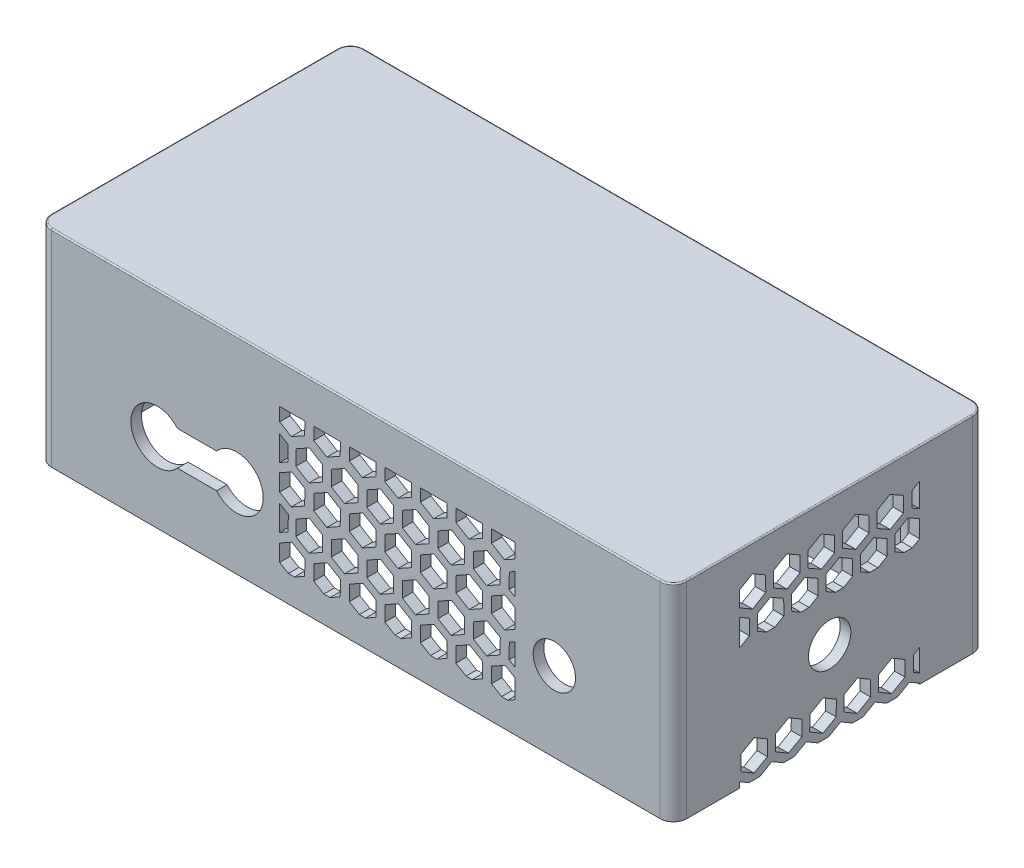
SolidWorks part; units mm, degrees
ref_plane "Front Plane" through (0, 0, 0) normal (0, 0, 1) x (1, 0, 0)
ref_plane "Top Plane" through (0, 0, 0) normal (0, 1, 0) x (1, 0, 0)
ref_plane "Right Plane" through (0, 0, 0) normal (1, 0, 0) x (0, 0, -1)
sketch "Sketch1" plane through (0, 0, 0) normal (0, 1, 0) x (1, 0, 0)
  line L1 (120, -59) -> (-120, -59)
  line L2 (120, -59) -> (120, 59)
  line L3 (120, 59) -> (-120, 59)
  line L4 (-120, -59) -> (-120, 59)
  line L5 (120, -59) -> (-120, 59) construction
  line L6 (120, 59) -> (-120, -59) construction
  point P0 (0, 0)
  dimension "D1" = 240
  dimension "D2" = 118
extrude "Boss-Extrude1" add sketch "Sketch1" along normal blind 78
sketch "Sketch2" plane through (0, 0, 0) normal (0, 1, 0) x (1, 0, 0)
  line L1 (-116, -55) -> (116, -55)
  line L2 (-116, -55) -> (-116, 55)
  line L3 (-116, 55) -> (116, 55)
  line L4 (116, -55) -> (116, 55)
  line L5 (-116, -55) -> (116, 55) construction
  line L6 (-116, 55) -> (116, -55) construction
  point P0 (0, 0)
  dimension "D1" = 232
  dimension "D2" = 110
extrude "Cut-Extrude1" cut sketch "Sketch2" along normal blind 70
sketch "Sketch3" plane through (0, 0, 0) normal (0, 1, 0) x (1, 0, 0)
  line L1 (-120, -59) -> (-106, -59)
  line L2 (-120, -59) -> (-120, -37)
  line L3 (-120, -37) -> (-106, -37)
  line L4 (-106, -59) -> (-106, -37)
  line L5 (-120, 59) -> (-106, 59)
  line L6 (-120, 59) -> (-120, 37)
  line L7 (-120, 37) -> (-106, 37)
  line L8 (-106, 59) -> (-106, 37)
  line L9 (120, -59) -> (106, -59)
  line L10 (120, -59) -> (120, -37)
  line L11 (120, -37) -> (106, -37)
  line L12 (106, -59) -> (106, -37)
  line L13 (120, 59) -> (106, 59)
  line L14 (120, 59) -> (120, 37)
  line L15 (120, 37) -> (106, 37)
  line L16 (106, 59) -> (106, 37)
  dimension "D1" = 22
  dimension "D2" = 14
  dimension "D3" = 14
  dimension "D4" = 22
  dimension "D5" = 22
  dimension "D6" = 14
  dimension "D7" = 14
  dimension "D8" = 22
extrude "Boss-Extrude2" add sketch "Sketch3" along normal blind 77.2
fillet "Fillet1" radius 2 8 edges at (106, 35, -55) (116, 35, -37) (116, 35, 37) (106, 35, 55) (-106, 35, -55) (-116, 35, -37) (-106, 35, 55) (-116, 35, 37)
fillet "Fillet2" radius 6.5 4 edges at (106, 35, -37) (106, 35, 37) (-106, 35, -37) (-106, 35, 37)
fillet "Fillet3" radius 5 4 edges at (120, 39, 59) (120, 39, -59) (-120, 39, -59) (-120, 39, 59)
sketch "Sketch4" plane through (0, 0, 0) normal (0, 0, 1) x (1, 0, 0)
  line L0 (-67.4007, 23.5) -> (-52.5993, 23.5)
  line L1 (-120, 78) -> (-120, 0) construction
  line L2 (-136.1714, 30) -> (133.1398, 30) construction
  line L7 (-67.4007, 36.5) -> (-52.5993, 36.5)
  circle A0 centre (75, 30) radius 8
  arc A1 (-67.4007, 36.5) -> (-67.4007, 23.5) centre (-75, 30) ccw
  arc A2 (-52.5993, 23.5) -> (-52.5993, 36.5) centre (-45, 30) ccw
  dimension "D1" = 45
  dimension "D2" = 195
extrude "Side Lidar and Sonar holes" cut sketch "Sketch4" against normal through all both and the other way through all
sketch "Sketch5" plane through (0, 0, 0) normal (0, 0, 1) x (1, 0, 0)
  line L0 (-12.5736, 29.0672) -> (-17.5522, 32.0521)
  line L1 (-19.2427, 17.9082) -> (-24.1944, 20.877)
  line L2 (-17.5522, 32.0521) -> (-22.5992, 29.2483)
  line L3 (-28.7882, 11.9716) -> (-28.7882, 63)
  line L4 (-28.7882, 63) -> (60.0514, 63)
  line L5 (-25.4998, 10) -> (57.3982, 10)
  line L6 (60.0514, 11.474) -> (60.0514, 63)
  line L7 (-24.1944, 20.877) -> (-28.7882, 18.3249)
  line L8 (-25.6128, 52.1399) -> (-28.7882, 54.0438)
  line L9 (-28.7882, 11.9716) -> (-25.4998, 10)
  line L10 (-23.1818, 10) -> (-19.338, 12.1354)
  line L11 (-19.338, 12.1354) -> (-19.2427, 17.9082)
  line L12 (-22.5992, 29.2483) -> (-22.6944, 23.4756)
  line L13 (-22.6944, 23.4756) -> (-17.7158, 20.4906)
  line L14 (-17.7158, 20.4906) -> (-12.6689, 23.2944)
  line L15 (-12.6689, 23.2944) -> (-12.5736, 29.0672)
  line L16 (0.8564, 29.0672) -> (-4.1222, 32.0521)
  line L17 (-5.8127, 17.9082) -> (-10.7644, 20.877)
  line L18 (-4.1222, 32.0521) -> (-9.1692, 29.2483)
  line L19 (-10.7644, 20.877) -> (-15.8114, 18.0732)
  line L20 (-15.8114, 18.0732) -> (-15.9066, 12.3004)
  line L21 (-15.9066, 12.3004) -> (-12.0698, 10)
  line L22 (-9.7518, 10) -> (-5.908, 12.1354)
  line L23 (-5.908, 12.1354) -> (-5.8127, 17.9082)
  line L24 (-9.1692, 29.2483) -> (-9.2644, 23.4756)
  line L25 (-9.2644, 23.4756) -> (-4.2858, 20.4906)
  line L26 (-4.2858, 20.4906) -> (0.7611, 23.2944)
  line L27 (0.7611, 23.2944) -> (0.8564, 29.0672)
  line L28 (14.2864, 29.0672) -> (9.3078, 32.0521)
  line L29 (7.6173, 17.9082) -> (2.6656, 20.877)
  line L30 (9.3078, 32.0521) -> (4.2608, 29.2483)
  line L31 (2.6656, 20.877) -> (-2.3814, 18.0732)
  line L32 (-2.3814, 18.0732) -> (-2.4766, 12.3004)
  line L33 (-2.4766, 12.3004) -> (1.3602, 10)
  line L34 (3.6782, 10) -> (7.522, 12.1354)
  line L35 (7.522, 12.1354) -> (7.6173, 17.9082)
  line L36 (4.2608, 29.2483) -> (4.1656, 23.4756)
  line L37 (4.1656, 23.4756) -> (9.1442, 20.4906)
  line L38 (9.1442, 20.4906) -> (14.1911, 23.2944)
  line L39 (14.1911, 23.2944) -> (14.2864, 29.0672)
  line L40 (27.7164, 29.0672) -> (22.7378, 32.0521)
  line L41 (21.0473, 17.9082) -> (16.0956, 20.877)
  line L42 (22.7378, 32.0521) -> (17.6908, 29.2483)
  line L43 (16.0956, 20.877) -> (11.0486, 18.0732)
  line L44 (11.0486, 18.0732) -> (10.9534, 12.3004)
  line L45 (10.9534, 12.3004) -> (14.7902, 10)
  line L46 (17.1082, 10) -> (20.952, 12.1354)
  line L47 (20.952, 12.1354) -> (21.0473, 17.9082)
  line L48 (17.6908, 29.2483) -> (17.5956, 23.4756)
  line L49 (17.5956, 23.4756) -> (22.5742, 20.4906)
  line L50 (22.5742, 20.4906) -> (27.6211, 23.2944)
  line L51 (27.6211, 23.2944) -> (27.7164, 29.0672)
  line L52 (41.1464, 29.0672) -> (36.1678, 32.0521)
  line L53 (34.4773, 17.9082) -> (29.5256, 20.877)
  line L54 (36.1678, 32.0521) -> (31.1208, 29.2483)
  line L55 (29.5256, 20.877) -> (24.4786, 18.0732)
  line L56 (24.4786, 18.0732) -> (24.3834, 12.3004)
  line L57 (24.3834, 12.3004) -> (28.2202, 10)
  line L58 (30.5382, 10) -> (34.382, 12.1354)
  line L59 (34.382, 12.1354) -> (34.4773, 17.9082)
  line L60 (31.1208, 29.2483) -> (31.0256, 23.4756)
  line L61 (31.0256, 23.4756) -> (36.0042, 20.4906)
  line L62 (36.0042, 20.4906) -> (41.0511, 23.2944)
  line L63 (41.0511, 23.2944) -> (41.1464, 29.0672)
  line L64 (54.5764, 29.0672) -> (49.5978, 32.0521)
  line L65 (47.9073, 17.9082) -> (42.9556, 20.877)
  line L66 (49.5978, 32.0521) -> (44.5508, 29.2483)
  line L67 (42.9556, 20.877) -> (37.9086, 18.0732)
  line L68 (37.9086, 18.0732) -> (37.8134, 12.3004)
  line L69 (37.8134, 12.3004) -> (41.6502, 10)
  line L70 (43.9682, 10) -> (47.812, 12.1354)
  line L71 (47.812, 12.1354) -> (47.9073, 17.9082)
  line L72 (44.5508, 29.2483) -> (44.4556, 23.4756)
  line L73 (44.4556, 23.4756) -> (49.4342, 20.4906)
  line L74 (49.4342, 20.4906) -> (54.4811, 23.2944)
  line L75 (54.4811, 23.2944) -> (54.5764, 29.0672)
  line L77 (60.0514, 18.6791) -> (56.3856, 20.877)
  line L78 (60.0514, 30.3986) -> (57.9808, 29.2483)
  line L79 (56.3856, 20.877) -> (51.3386, 18.0732)
  line L80 (51.3386, 18.0732) -> (51.2434, 12.3004)
  line L81 (51.2434, 12.3004) -> (55.0802, 10)
  line L82 (57.3982, 10) -> (60.0514, 11.474)
  line L84 (57.9808, 29.2483) -> (57.8856, 23.4756)
  line L85 (57.8856, 23.4756) -> (60.0514, 22.177)
  line L87 (-28.7882, 44.656) -> (-25.7081, 46.3672)
  line L88 (0.8564, 52.0672) -> (-4.1222, 55.0521)
  line L89 (-5.8127, 40.9082) -> (-10.7644, 43.877)
  line L90 (-4.1222, 55.0521) -> (-9.1692, 52.2483)
  line L91 (-10.7644, 43.877) -> (-15.8114, 41.0732)
  line L92 (-15.8114, 41.0732) -> (-15.9066, 35.3004)
  line L93 (-15.9066, 35.3004) -> (-10.9549, 32.3316)
  line L94 (-10.9549, 32.3316) -> (-5.908, 35.1354)
  line L95 (-5.908, 35.1354) -> (-5.8127, 40.9082)
  line L96 (-9.1692, 52.2483) -> (-9.2644, 46.4756)
  line L97 (-9.2644, 46.4756) -> (-4.2858, 43.4906)
  line L98 (-4.2858, 43.4906) -> (0.7611, 46.2944)
  line L99 (0.7611, 46.2944) -> (0.8564, 52.0672)
  line L100 (14.2864, 52.0672) -> (9.3078, 55.0521)
  line L101 (7.6173, 40.9082) -> (2.6656, 43.877)
  line L102 (9.3078, 55.0521) -> (4.2608, 52.2483)
  line L103 (2.6656, 43.877) -> (-2.3814, 41.0732)
  line L104 (-2.3814, 41.0732) -> (-2.4766, 35.3004)
  line L105 (-2.4766, 35.3004) -> (2.4751, 32.3316)
  line L106 (2.4751, 32.3316) -> (7.522, 35.1354)
  line L107 (7.522, 35.1354) -> (7.6173, 40.9082)
  line L108 (4.2608, 52.2483) -> (4.1656, 46.4756)
  line L109 (4.1656, 46.4756) -> (9.1442, 43.4906)
  line L110 (9.1442, 43.4906) -> (14.1911, 46.2944)
  line L111 (14.1911, 46.2944) -> (14.2864, 52.0672)
  line L112 (27.7164, 52.0672) -> (22.7378, 55.0521)
  line L113 (21.0473, 40.9082) -> (16.0956, 43.877)
  line L114 (22.7378, 55.0521) -> (17.6908, 52.2483)
  line L115 (16.0956, 43.877) -> (11.0486, 41.0732)
  line L116 (11.0486, 41.0732) -> (10.9534, 35.3004)
  line L117 (10.9534, 35.3004) -> (15.9051, 32.3316)
  line L118 (15.9051, 32.3316) -> (20.952, 35.1354)
  line L119 (20.952, 35.1354) -> (21.0473, 40.9082)
  line L120 (17.6908, 52.2483) -> (17.5956, 46.4756)
  line L121 (17.5956, 46.4756) -> (22.5742, 43.4906)
  line L122 (22.5742, 43.4906) -> (27.6211, 46.2944)
  line L123 (27.6211, 46.2944) -> (27.7164, 52.0672)
  line L124 (41.1464, 52.0672) -> (36.1678, 55.0521)
  line L125 (34.4773, 40.9082) -> (29.5256, 43.877)
  line L126 (36.1678, 55.0521) -> (31.1208, 52.2483)
  line L127 (29.5256, 43.877) -> (24.4786, 41.0732)
  line L128 (24.4786, 41.0732) -> (24.3834, 35.3004)
  line L129 (24.3834, 35.3004) -> (29.3351, 32.3316)
  line L130 (29.3351, 32.3316) -> (34.382, 35.1354)
  line L131 (34.382, 35.1354) -> (34.4773, 40.9082)
  line L132 (31.1208, 52.2483) -> (31.0256, 46.4756)
  line L133 (31.0256, 46.4756) -> (36.0042, 43.4906)
  line L134 (36.0042, 43.4906) -> (41.0511, 46.2944)
  line L135 (41.0511, 46.2944) -> (41.1464, 52.0672)
  line L136 (54.5764, 52.0672) -> (49.5978, 55.0521)
  line L137 (47.9073, 40.9082) -> (42.9556, 43.877)
  line L138 (49.5978, 55.0521) -> (44.5508, 52.2483)
  line L139 (42.9556, 43.877) -> (37.9086, 41.0732)
  line L140 (37.9086, 41.0732) -> (37.8134, 35.3004)
  line L141 (37.8134, 35.3004) -> (42.7651, 32.3316)
  line L142 (42.7651, 32.3316) -> (47.812, 35.1354)
  line L143 (47.812, 35.1354) -> (47.9073, 40.9082)
  line L144 (44.5508, 52.2483) -> (44.4556, 46.4756)
  line L145 (44.4556, 46.4756) -> (49.4342, 43.4906)
  line L146 (49.4342, 43.4906) -> (54.4811, 46.2944)
  line L147 (54.4811, 46.2944) -> (54.5764, 52.0672)
  line L148 (-25.7081, 46.3672) -> (-25.6128, 52.1399)
  line L149 (60.0514, 41.6791) -> (56.3856, 43.877)
  line L150 (60.0514, 53.3986) -> (57.9808, 52.2483)
  line L151 (56.3856, 43.877) -> (51.3386, 41.0732)
  line L152 (51.3386, 41.0732) -> (51.2434, 35.3004)
  line L153 (51.2434, 35.3004) -> (56.1951, 32.3316)
  line L154 (56.1951, 32.3316) -> (60.0514, 34.474)
  line L155 (-25.5041, 29.3213) -> (-28.7882, 31.2903)
  line L156 (57.9808, 52.2483) -> (57.8856, 46.4756)
  line L157 (57.8856, 46.4756) -> (60.0514, 45.177)
  line L163 (-28.7882, 21.7771) -> (-25.5994, 23.5486)
  line L164 (-15.8291, 63) -> (-15.9066, 58.3004)
  line L165 (-15.9066, 58.3004) -> (-10.9549, 55.3316)
  line L166 (-10.9549, 55.3316) -> (-5.908, 58.1354)
  line L167 (-5.908, 58.1354) -> (-5.8277, 63)
  line L173 (-25.5994, 23.5486) -> (-25.5041, 29.3213)
  line L176 (-2.3991, 63) -> (-2.4766, 58.3004)
  line L177 (-2.4766, 58.3004) -> (2.4751, 55.3316)
  line L178 (2.4751, 55.3316) -> (7.522, 58.1354)
  line L179 (7.522, 58.1354) -> (7.6023, 63)
  line L188 (11.0309, 63) -> (10.9534, 58.3004)
  line L189 (10.9534, 58.3004) -> (15.9051, 55.3316)
  line L190 (15.9051, 55.3316) -> (20.952, 58.1354)
  line L191 (20.952, 58.1354) -> (21.0323, 63)
  line L200 (24.4609, 63) -> (24.3834, 58.3004)
  line L201 (24.3834, 58.3004) -> (29.3351, 55.3316)
  line L202 (29.3351, 55.3316) -> (34.382, 58.1354)
  line L203 (34.382, 58.1354) -> (34.4623, 63)
  line L212 (37.8909, 63) -> (37.8134, 58.3004)
  line L213 (37.8134, 58.3004) -> (42.7651, 55.3316)
  line L214 (42.7651, 55.3316) -> (47.812, 58.1354)
  line L215 (47.812, 58.1354) -> (47.8923, 63)
  line L224 (51.3209, 63) -> (51.2434, 58.3004)
  line L225 (51.2434, 58.3004) -> (56.1951, 55.3316)
  line L226 (56.1951, 55.3316) -> (60.0514, 57.474)
  line L232 (-12.5736, 52.0672) -> (-17.5522, 55.0521)
  line L233 (-19.2427, 40.9082) -> (-24.1944, 43.877)
  line L234 (-17.5522, 55.0521) -> (-22.5992, 52.2483)
  line L235 (-24.1944, 43.877) -> (-28.7882, 41.3249)
  line L237 (-28.7882, 34.9716) -> (-24.3849, 32.3316)
  line L238 (-24.3849, 32.3316) -> (-19.338, 35.1354)
  line L239 (-19.338, 35.1354) -> (-19.2427, 40.9082)
  line L240 (-22.5992, 52.2483) -> (-22.6944, 46.4756)
  line L241 (-22.6944, 46.4756) -> (-17.7158, 43.4906)
  line L242 (-17.7158, 43.4906) -> (-12.6689, 46.2944)
  line L243 (-12.6689, 46.2944) -> (-12.5736, 52.0672)
  line L249 (-28.7882, 57.9716) -> (-24.3849, 55.3316)
  line L250 (-24.3849, 55.3316) -> (-19.338, 58.1354)
  line L251 (-19.338, 58.1354) -> (-19.2577, 63)
  line L256 (61.2896, 15.0218) -> (61.3373, 17.9082) [skipped]
  line L257 (68.0064, 29.0672) -> (63.0278, 32.0521) [skipped]
  line L258 (62.8642, 20.4906) -> (67.9111, 23.2944) [skipped]
  line L259 (67.9111, 23.2944) -> (68.0064, 29.0672) [skipped]
  line L260 (61.2896, 38.0218) -> (61.3373, 40.9082) [skipped]
  line L261 (68.0064, 52.0672) -> (63.0278, 55.0521) [skipped]
  line L262 (67.9111, 46.2944) -> (68.0064, 52.0672) [skipped]
  line L263 (62.8642, 43.4906) -> (67.9111, 46.2944) [skipped]
  line L264 (-29.2414, 18.0732) -> (-29.289, 15.1868) [skipped]
  line L265 (-24.1944, 66.877) -> (-26.7179, 65.4751) [skipped]
  line L266 (-19.2427, 63.9082) -> (-21.7186, 65.3926) [skipped]
  line L267 (-10.7644, 66.877) -> (-13.2879, 65.4751) [skipped]
  line L268 (-5.8127, 63.9082) -> (-8.2886, 65.3926) [skipped]
  line L269 (2.6656, 66.877) -> (0.1421, 65.4751) [skipped]
  line L270 (7.6173, 63.9082) -> (2.6656, 66.877) [skipped]
  line L271 (16.0956, 66.877) -> (13.5721, 65.4751) [skipped]
  line L272 (21.0473, 63.9082) -> (18.5714, 65.3926) [skipped]
  line L273 (29.5256, 66.877) -> (27.0021, 65.4751) [skipped]
  line L274 (34.4773, 63.9082) -> (32.0014, 65.3926) [skipped]
  line L275 (42.9556, 66.877) -> (40.4321, 65.4751) [skipped]
  line L276 (47.9073, 63.9082) -> (45.4314, 65.3926) [skipped]
  line L277 (56.3856, 66.877) -> (53.8621, 65.4751) [skipped]
  line L278 (61.3373, 63.9082) -> (58.8614, 65.3926) [skipped]
  line L279 (61.242, 58.1354) -> (61.2896, 61.0218) [skipped]
  line L280 (0.8564, 75.0672) -> (-4.1222, 78.0521) [skipped]
  line L281 (-4.1222, 78.0521) -> (-9.1692, 75.2483) [skipped]
  line L282 (-9.1692, 75.2483) -> (-9.2644, 69.4756) [skipped]
  line L283 (-9.2644, 69.4756) -> (-4.2858, 66.4906) [skipped]
  line L284 (-4.2858, 66.4906) -> (0.7611, 69.2944) [skipped]
  line L285 (0.7611, 69.2944) -> (0.8564, 75.0672) [skipped]
  line L286 (14.2864, 75.0672) -> (9.3078, 78.0521) [skipped]
  line L287 (9.3078, 78.0521) -> (4.2608, 75.2483) [skipped]
  line L288 (4.2608, 75.2483) -> (4.1656, 69.4756) [skipped]
  line L289 (4.1656, 69.4756) -> (9.1442, 66.4906) [skipped]
  line L290 (9.1442, 66.4906) -> (14.1911, 69.2944) [skipped]
  line L291 (14.1911, 69.2944) -> (14.2864, 75.0672) [skipped]
  line L292 (27.7164, 75.0672) -> (22.7378, 78.0521) [skipped]
  line L293 (22.7378, 78.0521) -> (17.6908, 75.2483) [skipped]
  line L294 (17.6908, 75.2483) -> (17.5956, 69.4756) [skipped]
  line L295 (17.5956, 69.4756) -> (22.5742, 66.4906) [skipped]
  line L296 (22.5742, 66.4906) -> (27.6211, 69.2944) [skipped]
  line L297 (27.6211, 69.2944) -> (27.7164, 75.0672) [skipped]
  line L298 (41.1464, 75.0672) -> (36.1678, 78.0521) [skipped]
  line L299 (36.1678, 78.0521) -> (31.1208, 75.2483) [skipped]
  line L300 (31.1208, 75.2483) -> (31.0256, 69.4756) [skipped]
  line L301 (31.0256, 69.4756) -> (36.0042, 66.4906) [skipped]
  line L302 (36.0042, 66.4906) -> (41.0511, 69.2944) [skipped]
  line L303 (41.0511, 69.2944) -> (41.1464, 75.0672) [skipped]
  line L304 (54.5764, 75.0672) -> (49.5978, 78.0521) [skipped]
  line L305 (49.5978, 78.0521) -> (44.5508, 75.2483) [skipped]
  line L306 (44.5508, 75.2483) -> (44.4556, 69.4756) [skipped]
  line L307 (44.4556, 69.4756) -> (49.4342, 66.4906) [skipped]
  line L308 (49.4342, 66.4906) -> (54.4811, 69.2944) [skipped]
  line L309 (54.4811, 69.2944) -> (54.5764, 75.0672) [skipped]
  line L310 (68.0064, 75.0672) -> (63.0278, 78.0521) [skipped]
  line L311 (63.0278, 78.0521) -> (57.9808, 75.2483) [skipped]
  line L312 (57.9808, 75.2483) -> (57.8856, 69.4756) [skipped]
  line L313 (57.8856, 69.4756) -> (62.8642, 66.4906) [skipped]
  line L314 (62.8642, 66.4906) -> (67.9111, 69.2944) [skipped]
  line L315 (67.9111, 69.2944) -> (68.0064, 75.0672) [skipped]
  line L316 (-12.5736, 75.0672) -> (-17.5522, 78.0521) [skipped]
  line L317 (-17.5522, 78.0521) -> (-22.5992, 75.2483) [skipped]
  line L318 (-22.5992, 75.2483) -> (-22.6944, 69.4756) [skipped]
  line L319 (-22.6944, 69.4756) -> (-17.7158, 66.4906) [skipped]
  line L320 (-17.7158, 66.4906) -> (-12.6689, 69.2944) [skipped]
  line L321 (-12.6689, 69.2944) -> (-12.5736, 75.0672) [skipped]
  arc A0 (-28.7882, 12.9218) -> (-28.7882, 17.2868) centre (-24.2897, 15.1043) ccw construction
  circle A1 centre (-17.6475, 26.2794) radius 5 construction
  circle A2 centre (-10.8597, 15.1043) radius 5 construction
  circle A3 centre (-4.2175, 26.2794) radius 5 construction
  circle A4 centre (2.5703, 15.1043) radius 5 construction
  circle A5 centre (9.2125, 26.2794) radius 5 construction
  circle A6 centre (16.0003, 15.1043) radius 5 construction
  circle A7 centre (22.6425, 26.2794) radius 5 construction
  circle A8 centre (29.4303, 15.1043) radius 5 construction
  circle A9 centre (36.0725, 26.2794) radius 5 construction
  circle A10 centre (42.8603, 15.1043) radius 5 construction
  circle A11 centre (49.5025, 26.2794) radius 5 construction
  arc A12 (60.0514, 18.3988) -> (60.0514, 11.8098) centre (56.2903, 15.1043) ccw construction
  arc A13 (60.0514, 30.3659) -> (60.0514, 22.193) centre (62.9325, 26.2794) ccw construction
  circle A14 centre (-10.8597, 38.1043) radius 5 construction
  circle A15 centre (-4.2175, 49.2794) radius 5 construction
  circle A16 centre (2.5703, 38.1043) radius 5 construction
  circle A17 centre (9.2125, 49.2794) radius 5 construction
  circle A18 centre (16.0003, 38.1043) radius 5 construction
  circle A19 centre (22.6425, 49.2794) radius 5 construction
  circle A20 centre (29.4303, 38.1043) radius 5 construction
  circle A21 centre (36.0725, 49.2794) radius 5 construction
  circle A22 centre (42.8603, 38.1043) radius 5 construction
  circle A23 centre (49.5025, 49.2794) radius 5 construction
  arc A24 (60.0514, 41.3988) -> (60.0514, 34.8098) centre (56.2903, 38.1043) ccw construction
  arc A25 (60.0514, 53.3659) -> (60.0514, 45.193) centre (62.9325, 49.2794) ccw construction
  arc A26 (-15.4864, 63) -> (-6.233, 63) centre (-10.8597, 61.1043) ccw construction
  arc A28 (-2.0564, 63) -> (7.197, 63) centre (2.5703, 61.1043) ccw construction
  arc A30 (11.3736, 63) -> (20.627, 63) centre (16.0003, 61.1043) ccw construction
  arc A32 (24.8036, 63) -> (34.057, 63) centre (29.4303, 61.1043) ccw construction
  arc A34 (38.2336, 63) -> (47.487, 63) centre (42.8603, 61.1043) ccw construction
  arc A36 (51.6636, 63) -> (60.0514, 57.8098) centre (56.2903, 61.1043) ccw construction
  arc A38 (-28.7882, 35.9218) -> (-28.7882, 40.2868) centre (-24.2897, 38.1043) ccw construction
  circle A39 centre (-17.6475, 49.2794) radius 5 construction
  arc A40 (-28.7882, 58.9218) -> (-19.663, 63) centre (-24.2897, 61.1043) ccw construction
  arc A42 (-28.7882, 44.7266) -> (-28.7882, 53.9778) centre (-30.6867, 49.3522) ccw construction
  arc A43 (-28.7882, 21.8649) -> (-28.7882, 31.2023) centre (-30.578, 26.5336) ccw construction
  circle A46 centre (-4.2175, 72.2794) radius 5 construction
  circle A47 centre (9.2125, 72.2794) radius 5 construction
  circle A48 centre (22.6425, 72.2794) radius 5 construction
  circle A49 centre (36.0725, 72.2794) radius 5 construction
  circle A50 centre (49.5025, 72.2794) radius 5 construction
  circle A51 centre (62.9325, 72.2794) radius 5 construction
  circle A52 centre (-17.6475, 72.2794) radius 5 construction
  point P20 (-21.7186, 19.3926)
  dimension "D1" = 3
  dimension "D2" = 1.5
  dimension "D4" = 2.5986
  dimension "D5" = 1.6222
  dimension "D7" = 7
  dimension "D8" = 3
extrude "Side honeycomb" cut sketch "Sketch5" against normal through all both and the other way through all contours L10 L11 L1 L7 L3 L9 L5 | L14 L15 L0 L2 L12 L13 | L238 L239 L233 L235 L3 L237 | L242 L243 L232 L234 L240 L241 | L250 L251 L4 L3 L249 | L166 L167 L4 L164 L165 | L178 L179 L4 L176 L177 | L98 L99 L88 L90 L96 L97 | L106 L107 L101 L103 L104 L105 | L94 L95 L89 L91 L92 L93 | L22 L23 L17 L19 L20 L21 L5 | L34 L35 L29 L31 L32 L33 L5 | L38 L39 L28 L30 L36 L37 | L118 L119 L113 L115 L116 L117 | L110 L111 L100 L102 L108 L109 | L190 L191 L4 L188 L189 | L122 L123 L112 L114 L120 L121 | L130 L131 L125 L127 L128 L129 | L50 L51 L40 L42 L48 L49 | L46 L47 L41 L43 L44 L45 L5 | L58 L59 L53 L55 L56 L57 L5 | L62 L63 L52 L54 L60 L61 | L142 L143 L137 L139 L140 L141 | L134 L135 L124 L126 L132 L133 | L202 L203 L4 L200 L201 | L214 L215 L4 L212 L213 | L225 L226 L6 L4 L224 | L146 L147 L136 L138 L144 L145 | L153 L154 L6 L149 L151 L152 | L74 L75 L64 L66 L72 L73 | L70 L71 L65 L67 L68 L69 L5 | L5 L82 L6 L77 L79 L80 L81 | L84 L85 L6 L78 | L156 L157 L6 L150 | L87 L148 L8 L3 | L163 L173 L155 L3 | L24 L25 L26 L27 L16 L18
sketch "Sketch6" plane through (0, 0, 0) normal (1, 0, 0) x (0, 0, -1)
  line L0 (59, 78) -> (59, 0) construction
  line L1 (-54, 0) -> (54, 0) construction
  line L2 (67.1373, 30) -> (-67.1373, 30) construction
  circle A0 centre (0, 30) radius 8
  dimension "D1" = 59
  dimension "D2" = 30
extrude "Back Sonar" cut sketch "Sketch6" along normal blind 145
sketch "Sketch7" plane through (0, 0, 0) normal (1, 0, 0) x (0, 0, -1)
  line L0 (-34, 64.9032) -> (-34, 58.965)
  line L2 (-54, 0) -> (54, 0) construction
  line L3 (-34, 46) -> (-33.7633, 46)
  line L4 (34, 0) -> (34, 0.3416)
  line L7 (-59, 0) -> (-59, 78) construction
  line L8 (59, 78) -> (59, 0) construction
  line L9 (34, 47.6163) -> (34, 54.1712)
  line L11 (17.8738, 59.0369) -> (22.89, 56.1785)
  line L12 (24.693, 47.9651) -> (28.1414, 46)
  line L13 (31.2367, 46) -> (34, 47.6163)
  line L15 (34, 54.1712) -> (29.644, 56.6534)
  line L16 (29.644, 56.6534) -> (24.6604, 53.7385)
  line L17 (24.6604, 53.7385) -> (24.693, 47.9651)
  line L18 (22.89, 56.1785) -> (27.8736, 59.0934)
  line L19 (27.8736, 59.0934) -> (27.841, 64.8668)
  line L20 (27.841, 64.8668) -> (22.8248, 67.7253)
  line L21 (22.8248, 67.7253) -> (17.8412, 64.8103)
  line L22 (17.8412, 64.8103) -> (17.8738, 59.0369)
  line L23 (4.8738, 59.0369) -> (9.89, 56.1785)
  line L24 (11.693, 47.9651) -> (15.1414, 46)
  line L25 (18.2367, 46) -> (21.6928, 48.0215)
  line L26 (21.6928, 48.0215) -> (21.6602, 53.795)
  line L27 (21.6602, 53.795) -> (16.644, 56.6534)
  line L28 (16.644, 56.6534) -> (11.6604, 53.7385)
  line L29 (11.6604, 53.7385) -> (11.693, 47.9651)
  line L30 (9.89, 56.1785) -> (14.8736, 59.0934)
  line L31 (14.8736, 59.0934) -> (14.841, 64.8668)
  line L32 (14.841, 64.8668) -> (9.8248, 67.7253)
  line L33 (9.8248, 67.7253) -> (4.8412, 64.8103)
  line L34 (4.8412, 64.8103) -> (4.8738, 59.0369)
  line L35 (-8.1262, 59.0369) -> (-3.11, 56.1785)
  line L36 (-1.307, 47.9651) -> (2.1414, 46)
  line L37 (5.2367, 46) -> (8.6928, 48.0215)
  line L38 (8.6928, 48.0215) -> (8.6602, 53.795)
  line L39 (8.6602, 53.795) -> (3.644, 56.6534)
  line L40 (3.644, 56.6534) -> (-1.3396, 53.7385)
  line L41 (-1.3396, 53.7385) -> (-1.307, 47.9651)
  line L42 (-3.11, 56.1785) -> (1.8736, 59.0934)
  line L43 (1.8736, 59.0934) -> (1.841, 64.8668)
  line L44 (1.841, 64.8668) -> (-3.1752, 67.7253)
  line L45 (-3.1752, 67.7253) -> (-8.1588, 64.8103)
  line L46 (-8.1588, 64.8103) -> (-8.1262, 59.0369)
  line L47 (-21.1262, 59.0369) -> (-16.11, 56.1785)
  line L48 (-14.307, 47.9651) -> (-10.8586, 46)
  line L49 (-7.7633, 46) -> (-4.3072, 48.0215)
  line L50 (-4.3072, 48.0215) -> (-4.3398, 53.795)
  line L51 (-4.3398, 53.795) -> (-9.356, 56.6534)
  line L52 (-9.356, 56.6534) -> (-14.3396, 53.7385)
  line L53 (-14.3396, 53.7385) -> (-14.307, 47.9651)
  line L54 (-16.11, 56.1785) -> (-11.1264, 59.0934)
  line L55 (-11.1264, 59.0934) -> (-11.159, 64.8668)
  line L56 (-11.159, 64.8668) -> (-16.1752, 67.7253)
  line L57 (-16.1752, 67.7253) -> (-21.1588, 64.8103)
  line L58 (-21.1588, 64.8103) -> (-21.1262, 59.0369)
  line L59 (-34, 58.965) -> (-29.11, 56.1785)
  line L60 (-27.307, 47.9651) -> (-23.8586, 46)
  line L61 (-20.7633, 46) -> (-17.3072, 48.0215)
  line L62 (-17.3072, 48.0215) -> (-17.3398, 53.795)
  line L63 (-17.3398, 53.795) -> (-22.356, 56.6534)
  line L64 (-22.356, 56.6534) -> (-27.3396, 53.7385)
  line L65 (-27.3396, 53.7385) -> (-27.307, 47.9651)
  line L66 (-29.11, 56.1785) -> (-24.1264, 59.0934)
  line L67 (-24.1264, 59.0934) -> (-24.159, 64.8668)
  line L68 (-24.159, 64.8668) -> (-29.1752, 67.7253)
  line L69 (-29.1752, 67.7253) -> (-34, 64.9032)
  line L70 (31.1586, 64.8181) -> (31.1822, 59.0447)
  line L71 (31.1822, 59.0447) -> (34, 57.4332)
  line L73 (-33.7633, 46) -> (-30.3072, 48.0215)
  line L74 (-30.3072, 48.0215) -> (-30.3398, 53.795)
  line L75 (-30.3398, 53.795) -> (-34, 55.8807)
  line L78 (34, 66.4742) -> (31.1586, 64.8181)
  line L79 (-34, 55.8807) -> (-34, 46)
  line L80 (-23.8586, 46) -> (-20.7633, 46)
  line L81 (-10.8586, 46) -> (-7.7633, 46)
  line L82 (2.1414, 46) -> (5.2367, 46)
  line L83 (15.1414, 46) -> (18.2367, 46)
  line L86 (28.1414, 46) -> (31.2367, 46)
  line L87 (34, 57.4332) -> (34, 66.4742)
  line L89 (18.5253, 10.9146) -> (18.4841, 5.1412)
  line L98 (34, 0.3416) -> (30.1804, 2.5833)
  line L99 (30.1804, 2.5833) -> (25.6313, 0)
  line L100 (18.4841, 5.1412) -> (23.4633, 2.2188)
  line L101 (23.4633, 2.2188) -> (28.4838, 5.0698)
  line L102 (28.4838, 5.0698) -> (28.525, 10.8432)
  line L103 (28.525, 10.8432) -> (23.5457, 13.7656)
  line L104 (23.5457, 13.7656) -> (18.5253, 10.9146)
  line L105 (5.5253, 10.9146) -> (5.4841, 5.1412)
  line L112 (21.5821, 0) -> (17.1804, 2.5833)
  line L113 (17.1804, 2.5833) -> (12.6313, 0)
  line L114 (5.4841, 5.1412) -> (10.4633, 2.2188)
  line L115 (10.4633, 2.2188) -> (15.4838, 5.0698)
  line L116 (15.4838, 5.0698) -> (15.525, 10.8432)
  line L117 (15.525, 10.8432) -> (10.5457, 13.7656)
  line L118 (10.5457, 13.7656) -> (5.5253, 10.9146)
  line L119 (-7.4747, 10.9146) -> (-7.5159, 5.1412)
  line L126 (8.5821, 0) -> (4.1804, 2.5833)
  line L127 (4.1804, 2.5833) -> (-0.3687, 0)
  line L128 (-7.5159, 5.1412) -> (-2.5367, 2.2188)
  line L129 (-2.5367, 2.2188) -> (2.4838, 5.0698)
  line L130 (2.4838, 5.0698) -> (2.525, 10.8432)
  line L131 (2.525, 10.8432) -> (-2.4543, 13.7656)
  line L132 (-2.4543, 13.7656) -> (-7.4747, 10.9146)
  line L133 (-20.4747, 10.9146) -> (-20.5159, 5.1412)
  line L138 (-4.4179, 0) -> (-8.8196, 2.5833)
  line L139 (-8.8196, 2.5833) -> (-13.3687, 0)
  line L140 (-20.5159, 5.1412) -> (-15.5367, 2.2188)
  line L141 (-15.5367, 2.2188) -> (-10.5162, 5.0698)
  line L142 (-10.5162, 5.0698) -> (-10.475, 10.8432)
  line L143 (-10.475, 10.8432) -> (-15.4543, 13.7656)
  line L146 (-15.4543, 13.7656) -> (-20.4747, 10.9146)
  line L147 (-33.4747, 10.9146) -> (-33.5159, 5.1412)
  line L148 (-34, 2.1023) -> (-34, 0)
  line L149 (34, 3.6732) -> (34, 12.0902)
  line L152 (-17.4179, 0) -> (-21.8196, 2.5833)
  line L153 (-21.8196, 2.5833) -> (-26.3687, 0)
  line L154 (-33.5159, 5.1412) -> (-28.5367, 2.2188)
  line L155 (7.3819, 80.6077) -> (9.89, 79.1784) [skipped]
  line L156 (9.89, 79.1784) -> (12.3818, 80.6359) [skipped]
  line L157 (27.1522, 78.1959) -> (24.6604, 76.7385) [skipped]
  line L158 (21.6602, 76.7949) -> (19.1521, 78.2242) [skipped]
  line L159 (14.1522, 78.1959) -> (11.6604, 76.7385) [skipped]
  line L160 (34.6602, 76.7949) -> (32.1521, 78.2242) [skipped]
  line L161 (20.3819, 80.6077) -> (22.89, 79.1784) [skipped]
  line L162 (25.3818, 80.6359) -> (27.8737, 82.0934) [skipped]
  line L163 (17.8412, 87.8103) -> (17.8575, 84.9236) [skipped]
  line L164 (22.8248, 90.7253) -> (17.8412, 87.8103) [skipped]
  line L165 (27.841, 87.8668) -> (25.3329, 89.296) [skipped]
  line L166 (27.8573, 84.9801) -> (27.841, 87.8668) [skipped]
  line L168 (24.6767, 73.8518) -> (24.693, 70.9651) [skipped]
  line L170 (11.6767, 73.8518) -> (11.693, 70.9651) [skipped]
  line L172 (-1.3233, 73.8518) -> (-1.307, 70.9651) [skipped]
  line L174 (-14.3233, 73.8518) -> (-14.307, 70.9651) [skipped]
  line L176 (-40.3233, 73.8518) -> (-40.307, 70.9651) [skipped]
  line L177 (-37.8478, 78.1959) -> (-40.3396, 76.7385) [skipped]
  line L178 (-30.3398, 76.7949) -> (-32.8479, 78.2242) [skipped]
  line L179 (-24.8478, 78.1959) -> (-27.3396, 76.7385) [skipped]
  line L180 (14.8573, 84.9801) -> (14.841, 87.8668) [skipped]
  line L181 (14.841, 87.8668) -> (9.8248, 90.7253) [skipped]
  line L182 (9.8248, 90.7253) -> (4.8412, 87.8103) [skipped]
  line L183 (4.8412, 87.8103) -> (4.8738, 82.0369) [skipped]
  line L184 (-8.1262, 82.0369) -> (-5.6181, 80.6077) [skipped]
  line L185 (8.6602, 76.7949) -> (3.644, 79.6534) [skipped]
  line L186 (3.644, 79.6534) -> (-1.3396, 76.7384) [skipped]
  line L187 (-0.6182, 80.6359) -> (1.8737, 82.0934) [skipped]
  line L188 (1.8736, 82.0934) -> (1.841, 87.8668) [skipped]
  line L189 (1.841, 87.8668) -> (-3.1752, 90.7253) [skipped]
  line L190 (-3.1752, 90.7253) -> (-8.1588, 87.8103) [skipped]
  line L191 (-8.1588, 87.8103) -> (-8.1262, 82.0369) [skipped]
  line L192 (-21.1262, 82.0369) -> (-18.6181, 80.6077) [skipped]
  line L193 (-4.3398, 76.7949) -> (-6.8479, 78.2242) [skipped]
  line L194 (-11.8478, 78.1959) -> (-14.3396, 76.7385) [skipped]
  line L195 (-13.6182, 80.6359) -> (-11.1263, 82.0934) [skipped]
  line L196 (-11.1264, 82.0934) -> (-11.159, 87.8668) [skipped]
  line L197 (-11.159, 87.8668) -> (-16.1752, 90.7253) [skipped]
  line L198 (-16.1752, 90.7253) -> (-21.1588, 87.8103) [skipped]
  line L199 (-21.1588, 87.8103) -> (-21.1262, 82.0369) [skipped]
  line L200 (-34.1262, 82.0369) -> (-29.11, 79.1784) [skipped]
  line L201 (-17.3398, 76.7949) -> (-19.8479, 78.2242) [skipped]
  line L202 (-29.11, 79.1784) -> (-24.1264, 82.0934) [skipped]
  line L203 (-24.1264, 82.0934) -> (-24.159, 87.8668) [skipped]
  line L204 (-24.159, 87.8668) -> (-29.1752, 90.7253) [skipped]
  line L205 (-29.1752, 90.7253) -> (-34.1588, 87.8103) [skipped]
  line L206 (-34.1588, 87.8103) -> (-34.1262, 82.0369) [skipped]
  line L207 (-47.1262, 82.0369) -> (-42.11, 79.1784) [skipped]
  line L208 (-42.11, 79.1784) -> (-37.1264, 82.0934) [skipped]
  line L209 (-37.1264, 82.0934) -> (-37.159, 87.8668) [skipped]
  line L210 (-37.159, 87.8668) -> (-42.1752, 90.7253) [skipped]
  line L211 (-42.1752, 90.7253) -> (-47.1588, 87.8103) [skipped]
  line L212 (-47.1588, 87.8103) -> (-47.1262, 82.0369) [skipped]
  line L213 (-27.3233, 73.8518) -> (-27.307, 70.9651) [skipped]
  line L215 (-37.8478, 55.1959) -> (-40.3396, 53.7385) [skipped]
  line L216 (-40.3233, 50.8518) -> (-40.307, 47.9651) [skipped]
  line L217 (-40.307, 47.9651) -> (-35.2908, 45.1066) [skipped]
  line L218 (-37.1427, 61.9801) -> (-37.159, 64.8668) [skipped]
  line L219 (-44.667, 66.2678) -> (-47.1588, 64.8103) [skipped]
  line L220 (-47.1425, 61.9236) -> (-47.1262, 59.0369) [skipped]
  line L221 (-44.6181, 57.6077) -> (-42.11, 56.1785) [skipped]
  line L222 (-42.11, 56.1785) -> (-39.6182, 57.6359) [skipped]
  line L223 (-37.7989, 69.5358) -> (-35.2908, 68.1066) [skipped]
  line L224 (-39.6671, 66.2961) -> (-42.1752, 67.7253) [skipped]
  line L225 (-34.1588, 64.8103) -> (-34.1425, 61.9236) [skipped]
  line L226 (34.6765, 50.9082) -> (34.6602, 53.795) [skipped]
  line L227 (41.1821, 59.0856) -> (41.1703, 61.9723) [skipped]
  line L228 (41.1585, 64.8591) -> (38.6526, 66.2922) [skipped]
  line L229 (36.194, 56.1784) -> (38.6881, 57.632) [skipped]
  line L230 (-34, 68.8616) -> (-32.0537, 70) [skipped]
  line L231 (-28.5367, 2.2188) -> (-23.5162, 5.0698)
  line L232 (-23.5162, 5.0698) -> (-23.475, 10.8432)
  line L233 (-23.475, 10.8432) -> (-28.4543, 13.7656)
  line L234 (-28.4543, 13.7656) -> (-33.4747, 10.9146)
  line L240 (-30.4179, 0) -> (-34, 2.1023)
  line L245 (34, 0) -> (-34, 0)
  line L319 (31.7316, 10.802) -> (31.6904, 5.0287)
  line L320 (31.6904, 5.0287) -> (34, 3.6732)
  line L324 (34, 12.0902) -> (31.7316, 10.802)
  line L328 (35.1597, 22.661) -> (30.1804, 25.5833) [skipped]
  line L329 (17.1804, 25.5833) -> (14.6702, 24.1578) [skipped]
  line L330 (6.6701, 24.1222) -> (4.1804, 25.5833) [skipped]
  line L333 (5.5253, 33.9146) -> (5.4841, 28.1412) [skipped]
  line L334 (19.6701, 24.1222) -> (17.1804, 25.5833) [skipped]
  line L335 (5.4841, 28.1412) -> (10.4633, 25.2188) [skipped]
  line L336 (10.4633, 25.2188) -> (15.4838, 28.0698) [skipped]
  line L337 (15.4838, 28.0698) -> (15.525, 33.8432) [skipped]
  line L338 (15.525, 33.8432) -> (10.5457, 36.7656) [skipped]
  line L339 (10.5457, 36.7656) -> (5.5253, 33.9146) [skipped]
  line L340 (-7.4747, 33.9146) -> (-7.5159, 28.1412) [skipped]
  line L341 (4.1804, 25.5833) -> (1.6702, 24.1578) [skipped]
  line L342 (-7.5159, 28.1412) -> (-2.5367, 25.2188) [skipped]
  line L343 (-2.5367, 25.2188) -> (2.4838, 28.0698) [skipped]
  line L344 (2.4838, 28.0698) -> (2.525, 33.8432) [skipped]
  line L345 (2.525, 33.8432) -> (-2.4543, 36.7656) [skipped]
  line L346 (-2.4543, 36.7656) -> (-7.4747, 33.9146) [skipped]
  line L347 (-20.4747, 33.9146) -> (-20.5159, 28.1412) [skipped]
  line L348 (-6.3299, 24.1222) -> (-8.8196, 25.5833) [skipped]
  line L349 (-8.8196, 25.5833) -> (-11.3298, 24.1578) [skipped]
  line L350 (-20.5159, 28.1412) -> (-15.5367, 25.2188) [skipped]
  line L351 (-15.5367, 25.2188) -> (-10.5162, 28.0698) [skipped]
  line L352 (-10.5162, 28.0698) -> (-10.475, 33.8432) [skipped]
  line L353 (-10.475, 33.8432) -> (-15.4543, 36.7656) [skipped]
  line L354 (-15.4543, 36.7656) -> (-20.4747, 33.9146) [skipped]
  line L355 (-33.4747, 33.9146) -> (-33.5159, 28.1412) [skipped]
  line L356 (-19.3299, 24.1222) -> (-21.8196, 25.5833) [skipped]
  line L357 (-21.8196, 25.5833) -> (-24.3298, 24.1578) [skipped]
  line L358 (-33.5159, 28.1412) -> (-28.5367, 25.2188) [skipped]
  line L359 (-28.5367, 25.2188) -> (-23.5162, 28.0698) [skipped]
  line L360 (-23.5162, 28.0698) -> (-23.475, 33.8432) [skipped]
  line L361 (-23.475, 33.8432) -> (-28.4543, 36.7656) [skipped]
  line L362 (-28.4543, 36.7656) -> (-33.4747, 33.9146) [skipped]
  line L363 (-46.4747, 33.9146) -> (-46.5159, 28.1412) [skipped]
  line L364 (-32.3299, 24.1222) -> (-34.8196, 25.5833) [skipped]
  line L365 (-34.8196, 25.5833) -> (-39.84, 22.7323) [skipped]
  line L366 (-46.5159, 28.1412) -> (-41.5367, 25.2188) [skipped]
  line L367 (-41.5367, 25.2188) -> (-36.5162, 28.0698) [skipped]
  line L368 (-36.5162, 28.0698) -> (-36.475, 33.8432) [skipped]
  line L369 (-36.475, 33.8432) -> (-41.4543, 36.7656) [skipped]
  line L370 (-41.4543, 36.7656) -> (-46.4747, 33.9146) [skipped]
  line L371 (18.5253, 33.9146) -> (18.4841, 28.1412) [skipped]
  line L372 (30.1804, 25.5833) -> (27.6702, 24.1578) [skipped]
  line L373 (18.4841, 28.1412) -> (23.4633, 25.2188) [skipped]
  line L374 (23.4633, 25.2188) -> (28.4838, 28.0698) [skipped]
  line L375 (28.4838, 28.0698) -> (28.525, 33.8432) [skipped]
  line L376 (28.525, 33.8432) -> (23.5457, 36.7656) [skipped]
  line L377 (23.5457, 36.7656) -> (18.5253, 33.9146) [skipped]
  line L388 (-38.9646, 12.3044) -> (-41.4543, 13.7656) [skipped]
  line L389 (-43.9645, 12.3401) -> (-46.4747, 10.9146) [skipped]
  line L393 (-34.8196, 2.5833) -> (-37.3298, 1.1578) [skipped]
  line L394 (-36.5162, 5.0698) -> (-36.4956, 7.9565) [skipped]
  line L395 (-39.0264, 3.6443) -> (-36.5162, 5.0698) [skipped]
  line L396 (-44.0263, 3.68) -> (-41.5367, 2.2188) [skipped]
  line L397 (-46.4953, 8.0279) -> (-46.5159, 5.1412) [skipped]
  line L403 (35.1185, -6.1124) -> (35.1391, -3.2257) [skipped]
  line L404 (30.098, -8.9634) -> (35.1185, -6.1124) [skipped]
  line L405 (25.1188, -6.041) -> (27.6084, -7.5022) [skipped]
  line L406 (25.1394, -3.1543) -> (25.1188, -6.041) [skipped]
  line L407 (26.3865, 70) -> (29.7092, 68.1066) [skipped]
  line L408 (29.7092, 68.1066) -> (32.9463, 70) [skipped]
  line L409 (13.3865, 70) -> (16.7092, 68.1066) [skipped]
  line L410 (16.7092, 68.1066) -> (19.9463, 70) [skipped]
  line L411 (0.3865, 70) -> (3.7092, 68.1066) [skipped]
  line L412 (3.7092, 68.1066) -> (6.9463, 70) [skipped]
  line L413 (-12.6135, 70) -> (-9.2908, 68.1066) [skipped]
  line L414 (-9.2908, 68.1066) -> (-6.0537, 70) [skipped]
  line L415 (-25.6135, 70) -> (-22.2908, 68.1066) [skipped]
  line L416 (-22.2908, 68.1066) -> (-19.0537, 70) [skipped]
  arc A0 (30.7654, 46) -> (34, 48.3684) centre (29.6766, 50.88) ccw construction
  circle A1 centre (22.8574, 61.9519) radius 5 construction
  arc A2 (17.7654, 46) -> (15.5878, 46) centre (16.6766, 50.88) ccw construction
  circle A3 centre (9.8574, 61.9519) radius 5 construction
  arc A4 (4.7654, 46) -> (2.5878, 46) centre (3.6766, 50.88) ccw construction
  circle A5 centre (-3.1426, 61.9519) radius 5 construction
  arc A6 (-8.2346, 46) -> (-10.4122, 46) centre (-9.3234, 50.88) ccw construction
  circle A7 centre (-16.1426, 61.9519) radius 5 construction
  arc A8 (-21.2346, 46) -> (-23.4122, 46) centre (-22.3234, 50.88) ccw construction
  arc A9 (-34, 60.7663) -> (-34, 63.1374) centre (-29.1426, 61.9519) ccw construction
  arc A10 (-34, 46.0583) -> (-34, 55.7017) centre (-35.3234, 50.88) ccw construction
  arc A11 (34, 53.3917) -> (28.5878, 46) centre (29.6766, 50.88) ccw construction
  arc A12 (34, 66.4563) -> (34, 57.4475) centre (36.1704, 61.9519) ccw construction
  arc A13 (33.9894, 0) -> (26.2891, 0) centre (30.1392, -3.19) ccw construction
  circle A15 centre (23.5045, 7.9922) radius 5 construction
  arc A16 (20.9894, 0) -> (13.2891, 0) centre (17.1392, -3.19) ccw construction
  circle A17 centre (10.5045, 7.9922) radius 5 construction
  arc A18 (7.9894, 0) -> (0.2891, 0) centre (4.1392, -3.19) ccw construction
  circle A19 centre (-2.4955, 7.9922) radius 5 construction
  arc A20 (-5.0106, 0) -> (-12.7109, 0) centre (-8.8608, -3.19) ccw construction
  circle A21 centre (-15.4955, 7.9922) radius 5 construction
  arc A28 (32.1521, 78.2242) -> (27.1522, 78.1959) centre (29.6766, 73.88) ccw construction
  arc A29 (27.8573, 84.9801) -> (25.3329, 89.296) centre (22.8574, 84.9519) ccw construction
  arc A30 (-30.3235, 73.9082) -> (-32.8479, 78.2242) centre (-35.3234, 73.88) ccw construction
  arc A31 (-19.8479, 78.2242) -> (-24.8478, 78.1959) centre (-22.3234, 73.88) ccw construction
  arc A32 (19.1521, 78.2242) -> (14.1522, 78.1959) centre (16.6766, 73.88) ccw construction
  arc A33 (14.8573, 84.9801) -> (4.8575, 84.9236) centre (9.8574, 84.9519) ccw construction
  arc A34 (6.1521, 78.2242) -> (1.1522, 78.1959) centre (3.6766, 73.88) ccw construction
  circle A35 centre (-3.1426, 84.9519) radius 5 construction
  arc A36 (-6.8479, 78.2242) -> (-14.3233, 73.8517) centre (-9.3234, 73.88) ccw construction
  circle A37 centre (-16.1426, 84.9519) radius 5 construction
  circle A38 centre (-29.1426, 84.9519) radius 5 construction
  circle A39 centre (-42.1426, 84.9519) radius 5 construction
  arc A40 (-44.6181, 57.6077) -> (-39.6182, 57.6359) centre (-42.1426, 61.9519) ccw construction
  circle A41 centre (-28.4955, 7.9922) radius 5 construction
  arc A42 (-31.0106, 0) -> (-34, 1.7353) centre (-34.8608, -3.19) ccw construction
  arc A43 (-18.0106, 0) -> (-25.7109, 0) centre (-21.8608, -3.19) ccw construction
  arc A56 (34, 12.081) -> (34, 3.6784) centre (36.7109, 7.8797) ccw construction
  arc A63 (32.6701, 24.1222) -> (27.6702, 24.1578) centre (30.1392, 19.81) ccw construction
  arc A64 (19.6701, 24.1222) -> (14.6702, 24.1578) centre (17.1392, 19.81) ccw construction
  arc A65 (6.6701, 24.1222) -> (1.6702, 24.1578) centre (4.1392, 19.81) ccw construction
  circle A66 centre (10.5045, 30.9922) radius 5 construction
  circle A67 centre (-2.4955, 30.9922) radius 5 construction
  arc A68 (-6.3299, 24.1222) -> (-11.3298, 24.1578) centre (-8.8608, 19.81) ccw construction
  circle A69 centre (-15.4955, 30.9922) radius 5 construction
  arc A70 (-19.3299, 24.1222) -> (-24.3298, 24.1578) centre (-21.8608, 19.81) ccw construction
  circle A71 centre (-28.4955, 30.9922) radius 5 construction
  arc A72 (-32.3299, 24.1222) -> (-37.3298, 24.1578) centre (-34.8608, 19.81) ccw construction
  circle A73 centre (-41.4955, 30.9922) radius 5 construction
  circle A74 centre (23.5045, 30.9922) radius 5 construction
  arc A75 (-46.4953, 8.0279) -> (-44.0263, 3.68) centre (-41.4955, 7.9922) ccw construction
  arc A76 (-26.8606, -3.1543) -> (-24.3916, -7.5022) centre (-21.8608, -3.19) ccw construction
  dimension "D6" = 3
  dimension "D1" = 25
  dimension "D2" = 25
  dimension "D3" = 46
  dimension "D4" = 3
  dimension "D5" = 21.7253
  dimension "D7" = 6
  dimension "D8" = 2
  dimension "D9" = 6
  dimension "D10" = 2
extrude "Back Honeycomb" cut sketch "Sketch7" along normal through all contours L12 L86 L13 L9 L15 L16 L17 | L71 L87 L78 L70 | L21 L22 L11 L18 L19 L20 | L24 L83 L25 L26 L27 L28 L29 | L36 L82 L37 L38 L39 L40 L41 | L33 L34 L23 L30 L31 L32 | L45 L46 L35 L42 L43 L44 | L48 L81 L49 L50 L51 L52 L53 | L57 L58 L47 L54 L55 L56 | L68 L69 L0 L59 L66 L67 | L60 L80 L61 L62 L63 L64 L65 | L75 L79 L3 L73 L74 | L245 L240 L148 | L245 L152 L153 | L245 L138 L139 | L143 L146 L133 L140 L141 L142 | L233 L234 L147 L154 L231 L232 | L131 L132 L119 L128 L129 L130 | L149 L324 L319 L320 | L103 L104 L89 L100 L101 L102 | L245 L4 L98 L99 | L245 L112 L113 | L245 L126 L127 | L117 L118 L105 L114 L115 L116
fillet "Fillet4" radius 0.5 8 edges at (118.5355, 78, -57.5355) (120, 78, 0) (118.5355, 78, 57.5355) (0, 78, 59) (-118.5355, 78, 57.5355) (-120, 78, 0) (-118.5355, 78, -57.5355) (0, 78, -59)
fillet "Fillet6" radius 0.5 24 edges at (-115.4142, 70, -36.4142) (-113.25, 70, -37) (-107.9038, 70, -38.9038) (-106, 70, -48.25) (-105.4142, 70, -54.4142) (0, 70, -55) (105.4142, 70, -54.4142) (106, 70, -48.25) (107.9038, 70, -38.9038) (113.25, 70, -37) (115.4142, 70, -36.4142) (116, 70, 0) (115.4142, 70, 36.4142) (113.25, 70, 37) (107.9038, 70, 38.9038) (106, 70, 48.25) (105.4142, 70, 54.4142) (0, 70, 55) (-105.4142, 70, 54.4142) (-106, 70, 48.25) (-107.9038, 70, 38.9038) (-113.25, 70, 37) (-115.4142, 70, 36.4142) (-116, 70, 0)
